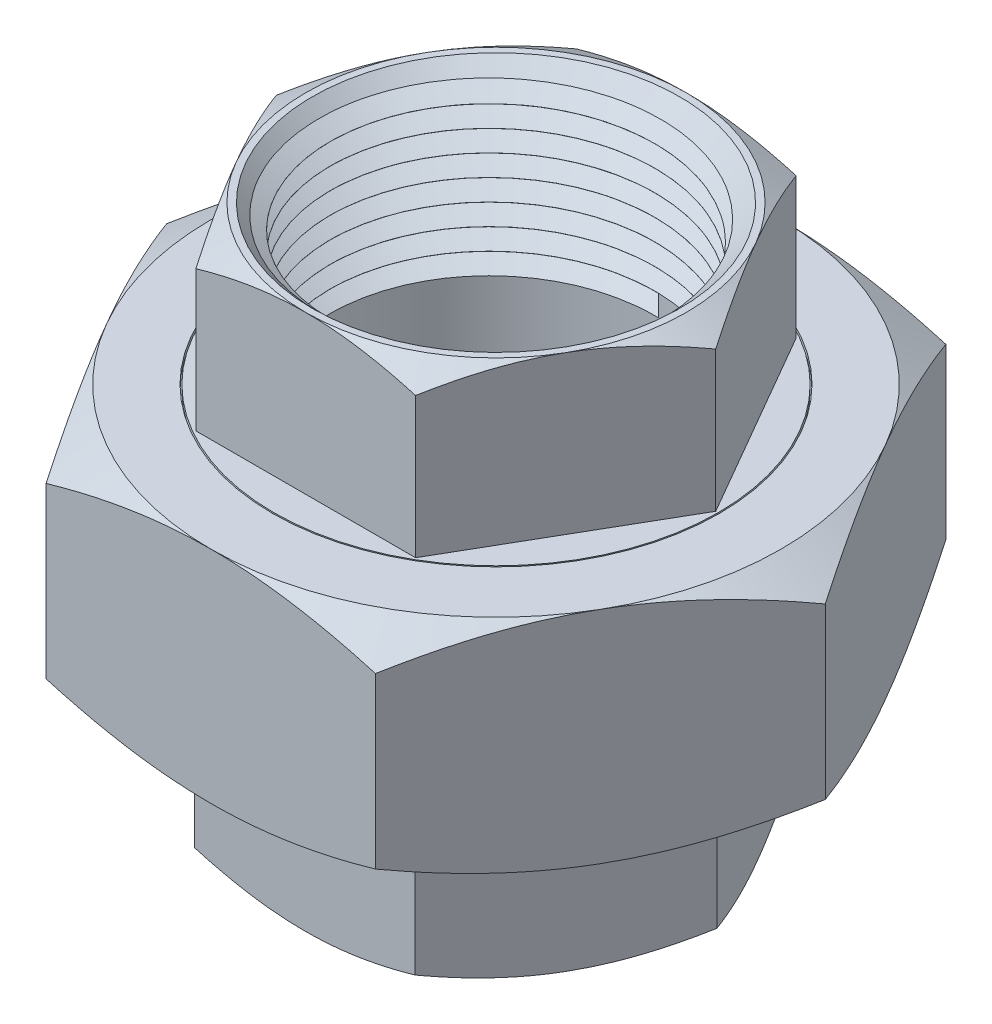
SolidWorks part; units mm, degrees
material "Cast Alloy Steel"
ref_plane "Front" through (0, 0, 0) normal (0, 0, 1) x (1, 0, 0)
ref_plane "Top" through (0, 0, 0) normal (0, 1, 0) x (1, 0, 0)
ref_plane "Right" through (0, 0, 0) normal (1, 0, 0) x (0, 0, -1)
sketch "Sketch1" plane through (0, 0, 0) normal (0, 1, 0) x (1, 0, 0)
  line L1 (30.946, 0) -> (15.473, 26.8)
  line L2 (15.473, 26.8) -> (-15.473, 26.8)
  line L3 (-15.473, 26.8) -> (-30.946, 0)
  line L4 (-30.946, 0) -> (-15.473, -26.8)
  line L5 (-15.473, -26.8) -> (15.473, -26.8)
  line L6 (15.473, -26.8) -> (30.946, 0)
  circle A0 centre (0, 0) radius 26.8 construction
  dimension "D1" = 53.6
extrude "Boss-Extrude1" add sketch "Sketch1" along normal blind 20.7
sketch "Sketch2" plane through (0, 20.7, 0) normal (0, 1, 0) x (1, 0, 0)
  circle A0 centre (0, 0) radius 21
  circle A1 centre (0, 0) radius 20.875
  dimension "D1" = 42
  dimension "D2" = 41.75
extrude "Cut-Extrude1" cut sketch "Sketch2" against normal blind 0.5
sketch "Sketch5" plane through (0, 20.7, 0) normal (0, 1, 0) x (1, 0, 0)
  line L1 (20.65, 0) -> (10.325, 17.8834)
  line L2 (10.325, 17.8834) -> (-10.325, 17.8834)
  line L3 (-10.325, 17.8834) -> (-20.65, 0)
  line L4 (-20.65, 0) -> (-10.325, -17.8834)
  line L5 (-10.325, -17.8834) -> (10.325, -17.8834)
  line L6 (10.325, -17.8834) -> (20.65, 0)
  circle A0 centre (0, 0) radius 17.8834 construction
  dimension "D1" = 41.3
extrude "Boss-Extrude7" add sketch "Sketch5" along normal blind 14.8
sketch "Sketch6" plane through (0, 0, 0) normal (0, -1, 0) x (1, 0, 0)
  line L1 (20.75, 0) -> (10.375, 17.97)
  line L2 (10.375, 17.97) -> (-10.375, 17.97)
  line L3 (-10.375, 17.97) -> (-20.75, 0)
  line L4 (-20.75, 0) -> (-10.375, -17.97)
  line L5 (-10.375, -17.97) -> (10.375, -17.97)
  line L6 (10.375, -17.97) -> (20.75, 0)
  circle A0 centre (0, 0) radius 17.97 construction
  dimension "D1" = 41.5
extrude "Boss-Extrude8" add sketch "Sketch6" along normal blind 14.8
sketch "Sketch7" plane through (0, 0, 0) normal (0, -1, 0) x (1, 0, 0)
  circle A0 centre (0, 0) radius 26.8
extrude "Cut-Extrude3" cut sketch "Sketch7" against normal blind 5 draft 60 flip side to cut
sketch "Sketch8" plane through (0, 20.7, 0) normal (0, 1, 0) x (1, 0, 0)
  circle A0 centre (0, 0) radius 26.8
extrude "Cut-Extrude4" cut sketch "Sketch8" against normal blind 5 draft 60 flip side to cut
sketch "Sketch9" plane through (0, -14.8, 0) normal (0, -1, 0) x (1, 0, 0)
  circle A0 centre (0, 0) radius 17.97
extrude "Cut-Extrude5" cut sketch "Sketch9" against normal blind 5 draft 60 flip side to cut
sketch "Sketch10" plane through (0, 35.5, 0) normal (0, 1, 0) x (1, 0, 0)
  circle A0 centre (0, 0) radius 17.8834
extrude "Cut-Extrude6" cut sketch "Sketch10" against normal blind 5 draft 60 flip side to cut
sketch "Sketch13" plane through (0, 0, 0) normal (0, -1, 0) x (1, 0, 0)
  circle A0 centre (0, 0) radius 23.25
  dimension "D1" = 46.5
sketch "Sketch12" plane through (0, 0, 0) normal (1, 0, 0) x (0, 0, -1)
  line L0 (0, 20.4252) -> (0, 0) construction
  line L1 (-23.25, 0) -> (23.25, 0) construction
  line L2 (23.25, 1.3357) -> (22.434, 0)
  line L3 (22.434, 0) -> (24.1044, 0)
  line L4 (13.4, 0) -> (26.8, 0) construction
  line L5 (24.1044, 0) -> (23.25, 1.3357)
  spline S0 degree 3 poles (26.8, 2.3937) (24.6079, 1.663) (22.3999, 1.061) (17.9375, 0.2281) (15.683, 0) (13.4, 0) knots 0 0 0 0 0.5 0.5 1 1 1 1 construction
sweep "Cut-Sweep1" cut profiles "Sketch12" path "Sketch13"
sketch "Sketch14" plane through (0, -14.8, 0) normal (0, -1, 0) x (1, 0, 0)
  circle A0 centre (0, 0) radius 15.25
  dimension "D1" = 30.5
extrude "Cut-Extrude7" cut sketch "Sketch14" against normal through all
sketch "Sketch15" plane through (0, -14.8, 0) normal (0, -1, 0) x (1, 0, 0)
  circle A0 centre (0, 0) radius 15.25 construction
  circle A1 centre (0, 0) radius 15.25
curve "Helix/Spiral1" pitch 2 height 15 turns 7.5
chamfer "Chamfer1" distance 2 angle 45 2 edges at (0, -14.8, -15.25) (0, 35.5, -15.25)
sketch "Sketch16" plane through (0, 0, 0) normal (1, 0, 0) x (0, 0, -1)
  line L0 (15.2056, -14.8) -> (15.2056, -12.81)
  line L1 (15.2056, -12.81) -> (16.9406, -13.805)
  line L2 (16.9406, -13.805) -> (15.2056, -14.8)
  line L3 (8.985, -14.8) -> (17.97, -14.8) construction
  dimension "D1" = 1.99
  dimension "D2" = 2
  dimension "D3" = 2
sweep "Cut-Sweep2" cut profiles "Sketch16" path "Helix/Spiral1"
sketch "Sketch17" plane through (0, 35.5, 0) normal (0, 1, 0) x (1, 0, 0)
  circle A0 centre (0, 0) radius 15.25 construction
  circle A1 centre (0, 0) radius 15.25
curve "Helix/Spiral2" pitch 2 height 15 turns 7.5
sketch "Sketch18" plane through (0, 0, 0) normal (1, 0, 0) x (0, 0, -1)
  line L0 (-15.25, 35.4996) -> (-15.25, 33.5096)
  line L1 (-15.25, 33.5096) -> (-16.9849, 34.5046)
  line L2 (-16.9849, 34.5046) -> (-15.25, 35.4996)
  spline S0 degree 3 poles (-15.25, 35.5) (-15.25, 35.4615) (-14.5641, 35.3836) (-11.6132, 35.2675) (-7.1298, 35.1512) (-1.7054, 35.0349) (3.944, 34.9186) (9.0729, 34.8023) (13.0045, 34.686) (15.2199, 34.5698) (15.4268, 34.4535) (13.5978, 34.3372) (9.9744, 34.2209) (5.0347, 34.1047) (-0.5695, 33.9884) (-6.0985, 33.8721) (-10.8227, 33.7558) (-14.1186, 33.6395) (-15.5514, 33.5233) (-14.9318, 33.407) (-12.3418, 33.2907) (-8.123, 33.1744) (-2.8323, 33.0581) (2.8323, 32.9419) (8.123, 32.8256) (12.3418, 32.7093) (14.9318, 32.593) (15.5514, 32.4767) (14.1186, 32.3605) (10.8227, 32.2442) (6.0985, 32.1279) (0.5695, 32.0116) (-5.0347, 31.8953) (-9.9744, 31.7791) (-13.5978, 31.6628) (-15.4268, 31.5465) (-15.2199, 31.4302) (-13.0045, 31.314) (-9.0729, 31.1977) (-3.944, 31.0814) (1.7054, 30.9651) (7.1298, 30.8488) (11.6132, 30.7326) (14.5641, 30.6163) (15.593, 30.5) (14.5641, 30.3837) (11.6132, 30.2674) (7.1298, 30.1512) (1.7054, 30.0349) (-3.944, 29.9186) (-9.0729, 29.8023) (-13.0045, 29.686) (-15.2199, 29.5698) (-15.4268, 29.4535) (-13.5978, 29.3372) (-9.9744, 29.2209) (-5.0347, 29.1047) (0.5695, 28.9884) (6.0985, 28.8721) (10.8227, 28.7558) (14.1186, 28.6395) (15.5514, 28.5233) (14.9318, 28.407) (12.3418, 28.2907) (8.123, 28.1744) (2.8323, 28.0581) (-2.8323, 27.9419) (-8.123, 27.8256) (-12.3418, 27.7093) (-14.9318, 27.593) (-15.5514, 27.4767) (-14.1186, 27.3605) (-10.8227, 27.2442) (-6.0985, 27.1279) (-0.5695, 27.0116) (5.0347, 26.8953) (9.9744, 26.7791) (13.5978, 26.6628) (15.4268, 26.5465) (15.2199, 26.4302) (13.0045, 26.314) (9.0729, 26.1977) (3.944, 26.0814) (-1.7054, 25.9651) (-7.1298, 25.8488) (-11.6132, 25.7326) (-14.5641, 25.6163) (-15.593, 25.5) (-14.5641, 25.3837) (-11.6132, 25.2674) (-7.1298, 25.1512) (-1.7054, 25.0349) (3.944, 24.9186) (9.0729, 24.8023) (13.0045, 24.686) (15.2199, 24.5698) (15.4268, 24.4535) (13.5978, 24.3372) (9.9744, 24.2209) (5.0347, 24.1047) (-0.5695, 23.9884) (-6.0985, 23.8721) (-10.8227, 23.7558) (-14.1186, 23.6395) (-15.5514, 23.5233) (-14.9318, 23.407) (-12.3418, 23.2907) (-8.123, 23.1744) (-2.8323, 23.0581) (2.8323, 22.9419) (8.123, 22.8256) (12.3418, 22.7093) (14.9318, 22.593) (15.5514, 22.4767) (14.1186, 22.3605) (10.8227, 22.2442) (6.0985, 22.1279) (0.5695, 22.0116) (-5.0347, 21.8953) (-9.9744, 21.7791) (-13.5978, 21.6628) (-15.4268, 21.5465) (-15.2199, 21.4302) (-13.0045, 21.314) (-9.0729, 21.1977) (-3.944, 21.0814) (1.7054, 20.9651) (7.1298, 20.8488) (11.6132, 20.7325) (14.5641, 20.6164) (15.25, 20.5385) (15.25, 20.5) knots 0 0 0 0 0.007752 0.015504 0.023256 0.031008 0.03876 0.046512 0.054264 0.062016 0.069767 0.077519 0.085271 0.093023 0.100775 0.108527 0.116279 0.124031 0.131783 0.139535 0.147287 0.155039 0.162791 0.170543 0.178295 0.186047 0.193798 0.20155 0.209302 0.217054 0.224806 0.232558 0.24031 0.248062 0.255814 0.263566 0.271318 0.27907 0.286822 0.294574 0.302326 0.310078 0.317829 0.325581 0.333333 0.341085 0.348837 0.356589 0.364341 0.372093 0.379845 0.387597 0.395349 0.403101 0.410853 0.418605 0.426357 0.434109 0.44186 0.449612 0.457364 0.465116 0.472868 0.48062 0.488372 0.496124 0.503876 0.511628 0.51938 0.527132 0.534884 0.542636 0.550388 0.55814 0.565891 0.573643 0.581395 0.589147 0.596899 0.604651 0.612403 0.620155 0.627907 0.635659 0.643411 0.651163 0.658915 0.666667 0.674419 0.682171 0.689922 0.697674 0.705426 0.713178 0.72093 0.728682 0.736434 0.744186 0.751938 0.75969 0.767442 0.775194 0.782946 0.790698 0.79845 0.806202 0.813953 0.821705 0.829457 0.837209 0.844961 0.852713 0.860465 0.868217 0.875969 0.883721 0.891473 0.899225 0.906977 0.914729 0.922481 0.930233 0.937984 0.945736 0.953488 0.96124 0.968992 0.976744 0.984496 0.992248 1 1 1 1 construction
  dimension "D1" = 1.99
  dimension "D2" = 2
  dimension "D3" = 2
sweep "Cut-Sweep3" cut profiles "Sketch18" path "Helix/Spiral2"
